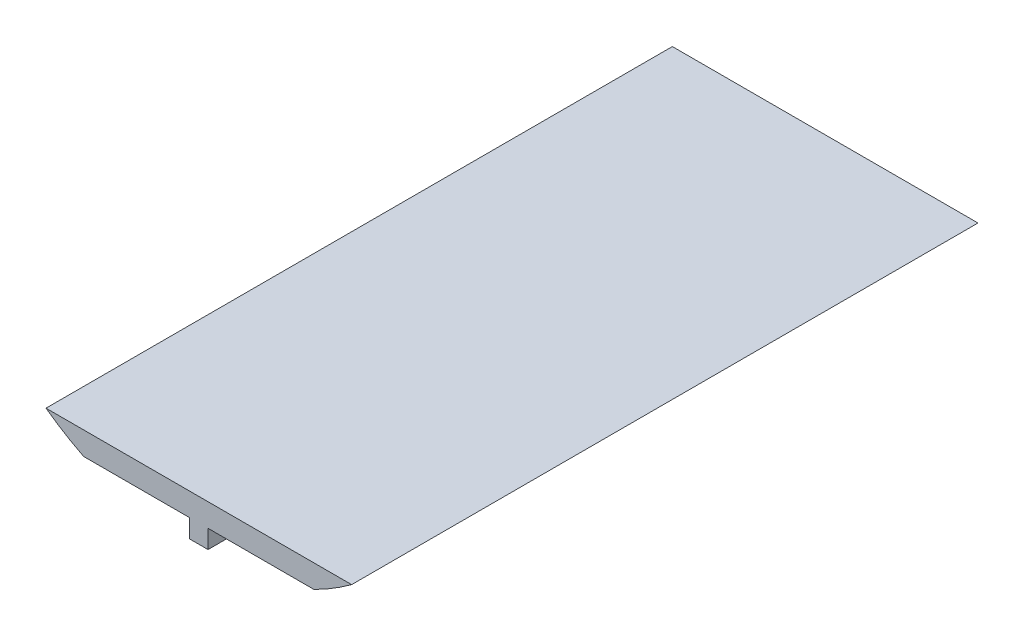
SolidWorks part; units mm, degrees
ref_plane "Front Plane" through (0, 0, 0) normal (0, 0, 1) x (1, 0, 0)
ref_plane "Top Plane" through (0, 0, 0) normal (0, 1, 0) x (1, 0, 0)
ref_plane "Right Plane" through (0, 0, 0) normal (1, 0, 0) x (0, 0, -1)
sketch "Sketch3" plane through (0, 0, 0) normal (0, 0, 1) x (1, 0, 0)
  circle A0 centre (0, 0) radius 71.12
  dimension "D1" = 142.24
extrude "Boss-Extrude2" add sketch "Sketch3" along normal blind 172.72
sketch "Sketch4" plane through (0, 0, 172.72) normal (0, 0, 1) x (1, 0, 0)
  line L0 (-31.75, -63.6395) -> (31.75, -63.6395)
  circle A0 centre (0, 0) radius 71.12 construction
  arc A1 (-31.75, -63.6395) -> (31.75, -63.6395) centre (0, 0) ccw
  dimension "D1" = 63.5
extrude "Cut-Extrude3" cut sketch "Sketch4" against normal through all
sketch "Sketch5" plane through (0, 0, 172.72) normal (0, 0, 1) x (1, 0, 0)
  line L0 (-66.3761, -25.5395) -> (66.3761, -25.5395)
  line L1 (31.75, -63.6395) -> (-31.75, -63.6395) construction
  arc A0 (31.75, -63.6395) -> (-31.75, -63.6395) centre (0, 0) ccw construction
  arc A1 (-66.3761, -25.5395) -> (66.3761, -25.5395) centre (0, 0) cw
  dimension "D1" = 38.1
extrude "Cut-Extrude4" cut sketch "Sketch5" against normal through all
sketch "Sketch7" plane through (0, -25.5395, 0) normal (0, 1, 0) x (1, 0, 0)
  line L0 (66.3761, 0) -> (66.3761, -172.72) construction
  line L1 (-66.3761, 0) -> (66.3761, 0)
  line L2 (-66.3761, 0) -> (-66.3761, -172.72)
  line L3 (-66.3761, -172.72) -> (66.3761, -172.72)
  line L4 (66.3761, 0) -> (66.3761, -172.72)
  dimension "D1" = 172.72
extrude "Cut-Extrude5" cut sketch "Sketch7" against normal blind 31.75
sketch "Sketch8" plane through (0, -63.6395, 0) normal (0, -1, 0) x (1, 0, 0)
  line L0 (31.75, 172.72) -> (-31.75, 172.72) construction
  line L1 (-2.54, 172.72) -> (2.54, 172.72)
  line L2 (-2.54, 172.72) -> (-2.54, 0)
  line L3 (-2.54, 0) -> (2.54, 0)
  line L4 (2.54, 172.72) -> (2.54, 0)
  line L5 (31.75, 0) -> (-31.75, 0) construction
  line L6 (31.75, 0) -> (31.75, 172.72) construction
  dimension "D1" = 5.08
  dimension "D2" = 29.21
extrude "Boss-Extrude3" add sketch "Sketch8" along normal blind 5.08
